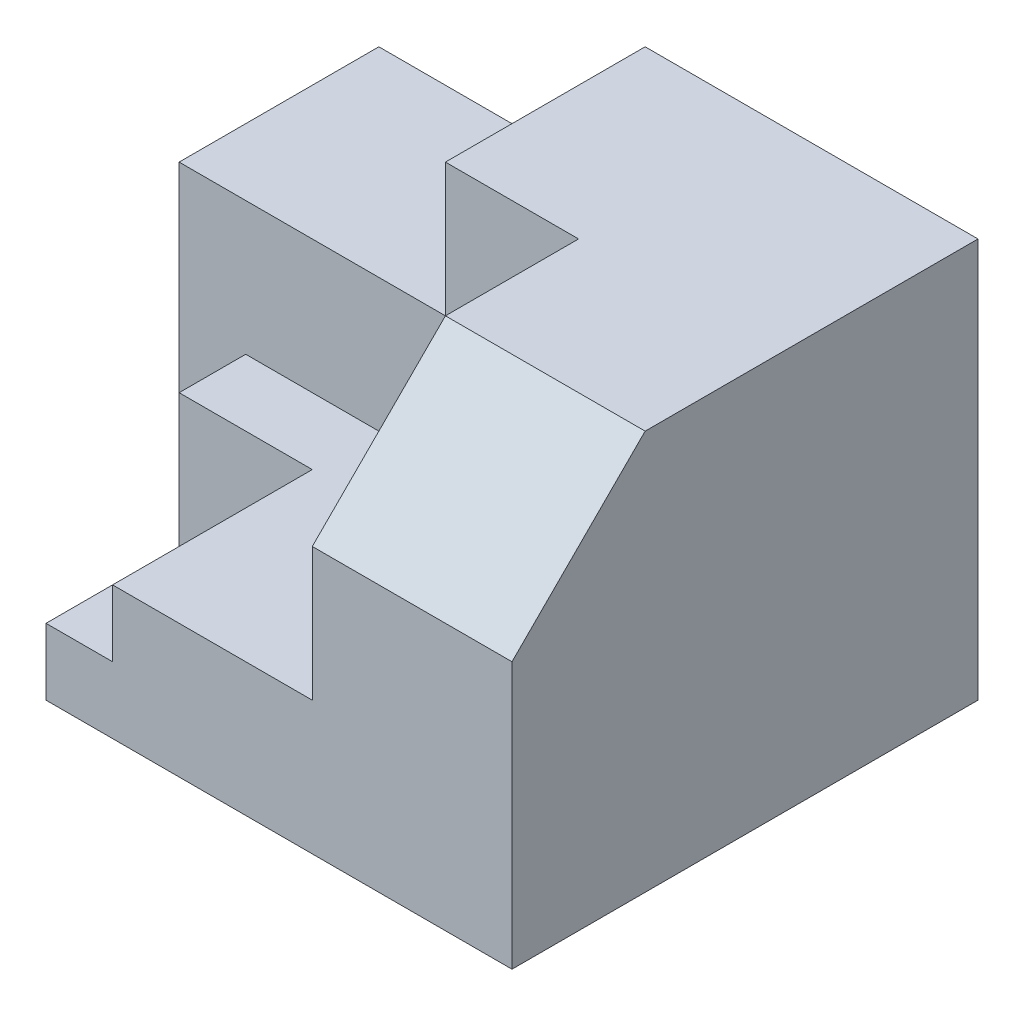
SolidWorks part; units mm, degrees
ref_plane "Front Plane" through (0, 0, 0) normal (0, 0, 1) x (1, 0, 0)
ref_plane "Top Plane" through (0, 0, 0) normal (0, 1, 0) x (1, 0, 0)
ref_plane "Right Plane" through (0, 0, 0) normal (1, 0, 0) x (0, 0, -1)
sketch "Sketch1" plane through (0, 0, 0) normal (0, 1, 0) x (1, 0, 0)
  line L1 (0, 0) -> (90, 0)
  line L2 (0, 0) -> (0, 70)
  line L3 (0, 70) -> (90, 70)
  line L4 (90, 0) -> (90, 70)
  dimension "D1" = 70
  dimension "D2" = 90
extrude "Boss-Extrude1" add sketch "Sketch1" along normal blind 60
sketch "Sketch2" plane through (0, 60, 0) normal (0, 1, 0) x (1, 0, 0)
  line L1 (0, 0) -> (60, 0)
  line L2 (0, 0) -> (0, 40)
  line L3 (0, 40) -> (60, 40)
  line L4 (60, 0) -> (60, 40)
  dimension "D1" = 40
  dimension "D2" = 60
extrude "Cut-Extrude1" cut sketch "Sketch2" against normal blind 40
sketch "Sketch3" plane through (0, 20, 0) normal (0, 1, 0) x (1, 0, 0)
  line L1 (0, 0) -> (30, 0)
  line L2 (0, 0) -> (0, 30)
  line L3 (0, 30) -> (30, 30)
  line L4 (30, 0) -> (30, 30)
  dimension "D1" = 30
  dimension "D2" = 30
extrude "Cut-Extrude2" cut sketch "Sketch3" against normal blind 10
sketch "Sketch4" plane through (0, 0, 0) normal (-1, 0, 0) x (0, 0, 1)
  line L1 (0, 0) -> (-30, 0)
  line L2 (0, 0) -> (0, 10)
  line L3 (0, 10) -> (-30, 10)
  line L4 (-30, 0) -> (-30, 10)
extrude "Cut-Extrude3" cut sketch "Sketch4" against normal blind 20
sketch "Sketch5" plane through (0, 0, 0) normal (-1, 0, 0) x (0, 0, 1)
  line L1 (-30, 0) -> (-40, 0)
  line L2 (-30, 0) -> (-30, 20)
  line L3 (-30, 20) -> (-40, 20)
  line L4 (-40, 0) -> (-40, 20)
extrude "Cut-Extrude4" cut sketch "Sketch5" against normal blind 10
sketch "Sketch7" plane through (0, 60, 0) normal (0, 1, 0) x (1, 0, 0)
  line L0 (90, 70) -> (0, 70) construction
  line L1 (0, 40) -> (40, 40)
  line L2 (0, 40) -> (0, 70)
  line L3 (0, 70) -> (40, 70)
  line L4 (40, 40) -> (40, 70)
  dimension "D1" = 40
extrude "Cut-Extrude5" cut sketch "Sketch7" against normal blind 20
chamfer "Chamfer1" distance 20 1 edges at (75, 60, 0)
